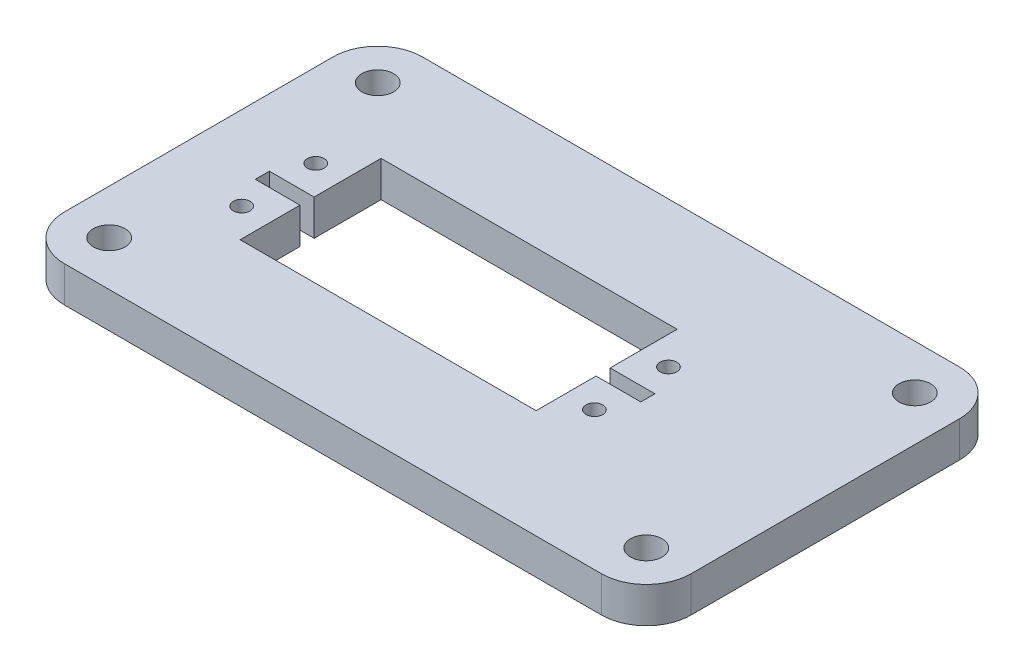
SolidWorks part; units mm, degrees
ref_plane "Front" through (0, 0, 0) normal (0, 0, 1) x (1, 0, 0)
ref_plane "Top" through (0, 0, 0) normal (0, 1, 0) x (1, 0, 0)
ref_plane "Right" through (0, 0, 0) normal (1, 0, 0) x (0, 0, -1)
sketch "Sketch1" plane through (0, 0, 0) normal (0, 1, 0) x (1, 0, 0)
  line L0 (-88.9, 0) -> (0, 0)
  line L2 (-31.025, -15.4) -> (-73.025, -15.4)
  line L3 (-73.025, -15.4) -> (-73.025, -35.4)
  line L4 (0, -50.8) -> (-88.9, -50.8)
  line L5 (-88.9, -50.8) -> (-88.9, 0)
  line L6 (-73.025, -35.4) -> (-31.025, -35.4)
  line L8 (-31.025, -15.4) -> (-31.025, -35.4)
  line L9 (0, 0) -> (0, -50.8)
  point P5 (-31.025, -25.4)
  point P10 (0, -25.4)
  dimension "D1" = 42
  dimension "D2" = 20
  dimension "D3" = 88.9
  dimension "D4" = 50.8
  dimension "D5" = 15.875
extrude "Boss-Extrude1" add sketch "Sketch1" along normal blind 5.08
hole_wizard "3/32 (0.09375) Diameter Hole1" positions "Sketch2" profile "Sketch3" hole size "3/32" standard "ANSI Inch" end condition through all
sketch "Sketch2" plane through (0, 5.08, 0) normal (0, 1, 0) x (1, 0, 0)
  line L1 (-77.044, -31.15) -> (-77.044, -20.65)
  line L3 (-73.025, -15.4) -> (-31.025, -15.4) construction
  line L5 (-52.025, -15.4) -> (-52.025, -35.4)
  line L6 (-31.025, -15.4) -> (-73.025, -15.4) construction
  line L7 (-73.025, -35.4) -> (-31.025, -35.4) construction
  point P0 (-77.044, -31.15)
  point P2 (-77.044, -20.65)
  point P10 (-77.044, -25.9)
  point P26 (-27.006, -31.15)
  point P27 (-27.006, -20.65)
  dimension "D1" = 10.5
  dimension "D2" = 50.038
  dimension "D3" = 10.5
sketch "Sketch3" plane through (-77.044, 5.08, 31.15) normal (1, 0, 0) x (0, 0, 1)
  line L0 (0, 0) -> (0, 5.08)
  line L1 (0, 5.08) -> (1.1906, 5.08)
  line L2 (1.1906, 5.08) -> (1.1906, 0)
  line L5 (1.1906, 0) -> (0, 0)
  line L11 (0, -6.35) -> (0, 107.95) construction
  dimension "Thru Hole Dia." = 2.3812
  dimension "Thru Hole Depth" = 5.08
sketch "Sketch4" plane through (0, 5.08, 0) normal (0, 1, 0) x (1, 0, 0)
  line L0 (-73.025, -35.4) -> (-73.025, -15.4) construction
  line L1 (-73.025, -24.9) -> (-79.375, -24.9)
  line L2 (-73.025, -24.9) -> (-73.025, -26.9)
  line L3 (-73.025, -26.9) -> (-79.375, -26.9)
  line L4 (-79.375, -24.9) -> (-79.375, -26.9)
  line L5 (-77.044, -31.15) -> (-77.044, -20.65) construction
  line L6 (-31.025, -35.4) -> (-31.025, -15.4) construction
  line L7 (-31.025, -24.9) -> (-24.675, -24.9)
  line L8 (-31.025, -24.9) -> (-31.025, -26.9)
  line L9 (-31.025, -26.9) -> (-24.675, -26.9)
  line L10 (-24.675, -24.9) -> (-24.675, -26.9)
  point P10 (-77.044, -25.9)
  point P11 (-79.375, -25.9)
  dimension "D1" = 2
  dimension "D2" = 6.35
extrude "Cut-Extrude1" cut sketch "Sketch4" against normal through all
fillet "Fillet2" radius 6.35 4 edges at (0, 2.54, 50.8) (0, 2.54, 0) (-88.9, 2.54, 50.8) (-88.9, 2.54, 0)
hole_wizard "#8 Clearance Hole1" positions "Sketch5" profile "Sketch6" hole size "#8" standard "ANSI Inch" end condition through all
sketch "Sketch5" plane through (0, 5.08, 0) normal (0, 1, 0) x (1, 0, 0)
  point P0 (-82.55, -6.35)
  point P3 (-82.55, -44.45)
  point P6 (-6.35, -6.35)
  point P9 (-6.35, -44.45)
sketch "Sketch6" plane through (-82.55, 5.08, 6.35) normal (1, 0, 0) x (0, 0, 1)
  line L0 (0, 0) -> (0, 5.08)
  line L1 (0, 5.08) -> (2.2479, 5.08)
  line L2 (2.2479, 5.08) -> (2.2479, 0)
  line L5 (2.2479, 0) -> (0, 0)
  line L11 (0, -6.35) -> (0, 107.95) construction
  dimension "Thru Hole Dia." = 4.4958
  dimension "Thru Hole Depth" = 5.08
